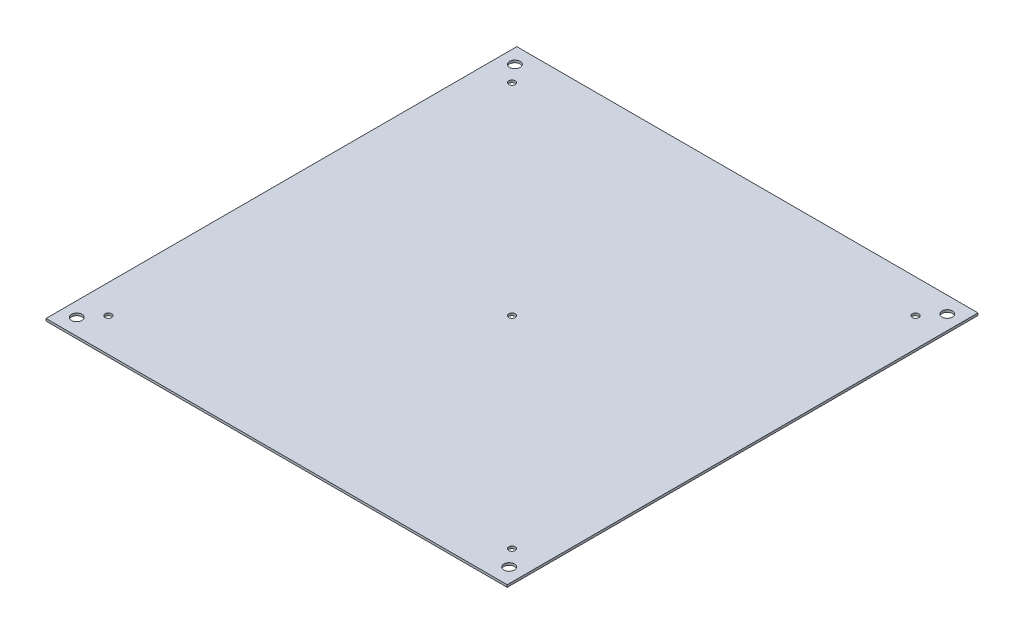
SolidWorks part; units mm, degrees
ref_plane "Front" through (0, 0, 0) normal (0, 0, 1) x (1, 0, 0)
ref_plane "Top" through (0, 0, 0) normal (0, 1, 0) x (1, 0, 0)
ref_plane "Right" through (0, 0, 0) normal (1, 0, 0) x (0, 0, -1)
sketch "Sketch1" plane through (0, 0, 0) normal (0, 1, 0) x (1, 0, 0)
  line L1 (120, 122.5) -> (-120, 122.5)
  line L2 (120, 122.5) -> (120, -122.5)
  line L3 (120, -122.5) -> (-120, -122.5)
  line L4 (-120, 122.5) -> (-120, -122.5)
  line L5 (0, -122.5) -> (0, 122.5) construction
  line L6 (120, 0) -> (-120, 0) construction
  point P0 (0, 0)
  dimension "D1" = 245
  dimension "D2" = 240
extrude "Boss-Extrude1" add sketch "Sketch1" along normal blind 1.2
hole_wizard "M3 Clearance Hole1" positions "Sketch2" profile "Sketch3" hole size "M3" standard "ANSI Metric" end condition through all
sketch "Sketch2" plane through (0, 1.2, 0) normal (0, 1, 0) x (1, 0, 0)
  line L1 (-105, -105) -> (105, -105)
  line L2 (-105, -105) -> (-105, 105)
  line L3 (-105, 105) -> (105, 105)
  line L4 (105, -105) -> (105, 105)
  line L5 (0, 105) -> (0, -105) construction
  line L6 (-105, 0) -> (105, 0) construction
  point P1 (0, 0)
  point P2 (105, 105)
  point P273 (-105, -105)
  point P274 (-105, 105)
  point P275 (105, -105)
  dimension "D1" = 210
sketch "Sketch3" plane through (0, 1.2, 0) normal (1, 0, 0) x (0, 0, 1)
  line L0 (0, 0) -> (0, 1.2)
  line L1 (0, 1.2) -> (1.7, 1.2)
  line L2 (1.7, 1.2) -> (1.7, 0)
  line L5 (1.7, 0) -> (0, 0)
  line L11 (0, -6.35) -> (0, 107.95) construction
  dimension "Thru Hole Dia." = 3.4
  dimension "Thru Hole Depth" = 1.2
hole_wizard "M5 Clearance Hole1" positions "Sketch4" profile "Sketch5" hole size "M5" standard "ANSI Metric" end condition through all
sketch "Sketch4" plane through (0, 0, 0) normal (0, -1, 0) x (-1, 0, 0)
  line L1 (112.5, 114) -> (-112.5, 114)
  line L2 (112.5, 114) -> (112.5, -114)
  line L3 (112.5, -114) -> (-112.5, -114)
  line L4 (-112.5, 114) -> (-112.5, -114)
  line L5 (-112.5, 0) -> (112.5, 0) construction
  point P0 (-112.5, -114)
  point P5 (112.5, 114)
  point P129 (112.5, -114)
  point P130 (-112.5, 114)
  dimension "D1" = 225
  dimension "D2" = 228
sketch "Sketch5" plane through (112.5, 0, 114) normal (1, 0, 0) x (0, 0, -1)
  line L0 (0, 0) -> (0, 1.2)
  line L1 (0, 1.2) -> (2.75, 1.2)
  line L2 (2.75, 1.2) -> (2.75, 0)
  line L5 (2.75, 0) -> (0, 0)
  line L11 (0, -6.35) -> (0, 107.95) construction
  dimension "Thru Hole Dia." = 5.5
  dimension "Thru Hole Depth" = 1.2
